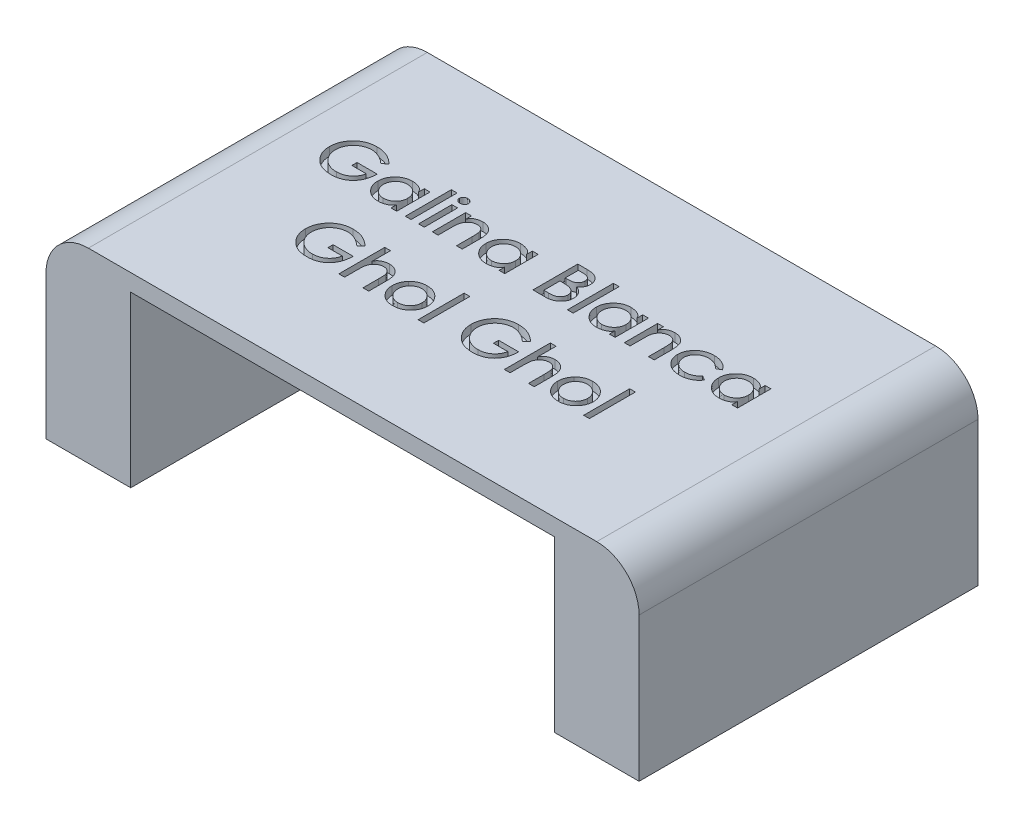
SolidWorks part; units mm, degrees
ref_plane "Front Plane" through (0, 0, 0) normal (0, 0, 1) x (1, 0, 0)
ref_plane "Top Plane" through (0, 0, 0) normal (0, 1, 0) x (1, 0, 0)
ref_plane "Right Plane" through (0, 0, 0) normal (1, 0, 0) x (0, 0, -1)
sketch "Sketch1" plane through (0, 0, 0) normal (0, 1, 0) x (1, 0, 0)
  line L1 (-35, 20) -> (35, 20)
  line L2 (-35, 20) -> (-35, -20)
  line L3 (-35, -20) -> (35, -20)
  line L4 (35, 20) -> (35, -20)
  line L5 (-35, 20) -> (35, -20) construction
  line L6 (-35, -20) -> (35, 20) construction
  point P0 (0, 0)
  dimension "D1" = 70
  dimension "D2" = 40
extrude "Boss-Extrude1" add sketch "Sketch1" along normal blind 2
sketch "Sketch2" plane through (0, 0, 0) normal (0, -1, 0) x (1, 0, 0)
  line L0 (35, -20) -> (-35, -20) construction
  line L1 (-35, 20) -> (-25, 20)
  line L2 (-35, 20) -> (-35, -20)
  line L3 (-35, -20) -> (-25, -20)
  line L4 (-25, 20) -> (-25, -20)
  line L5 (-61.3876, 0) -> (2.7293, 0) construction
  line L6 (35, 20) -> (25, 20)
  line L7 (35, 20) -> (35, -20)
  line L8 (35, -20) -> (25, -20)
  line L9 (25, 20) -> (25, -20)
  line L10 (-35, 20) -> (35, 20) construction
  line L11 (0, 31.618) -> (0, -35.7561) construction
  circle A0 centre (-30, 15) radius 1.75
  circle A1 centre (-30, -15) radius 1.75
  circle A2 centre (30, 15) radius 1.75
  circle A3 centre (30, -15) radius 1.75
  point P24 (0, 20)
  point P27 (-35, 0)
  point P28 (0, 0)
  point P29 (0, 0)
  point P30 (0, 0)
  dimension "D3" = 30
  dimension "D5" = 3.5
  dimension "D1" = 10
  dimension "D2" = 10
  dimension "D4" = 60
extrude "Boss-Extrude2" add sketch "Sketch2" along normal blind 20
sketch "Sketch3" plane through (0, 2, 0) normal (0, 1, 0) x (1, 0, 0)
  line L0 (-61.4581, 1.9645) -> (59.284, 1.9645) construction
  text T0 "<b>Galina Blanca</b>\r\n<b>Ghol Ghol</b>" font "Century Gothic" height in points 20
  point P3 (45.6026, -1.7332)
  point P4 (59.284, -2.2878)
  point P5 (-43.1417, -1.9181)
  point P6 (-52.3859, -1.7332)
  point P7 (-19.2917, 0)
  point P8 (-22.4347, 1.9645)
  point P9 (0, 0)
  point P10 (0, 0)
  point P11 (-61.4581, 1.9645)
  point P12 (0, 0)
  point P13 (0, 0)
  point P14 (0, 0)
extrude "Cut-Extrude1" cut sketch "Sketch3" against normal blind 1
fillet "Fillet2" radius 5 2 edges at (-35, 2, 0) (35, 2, 0)
